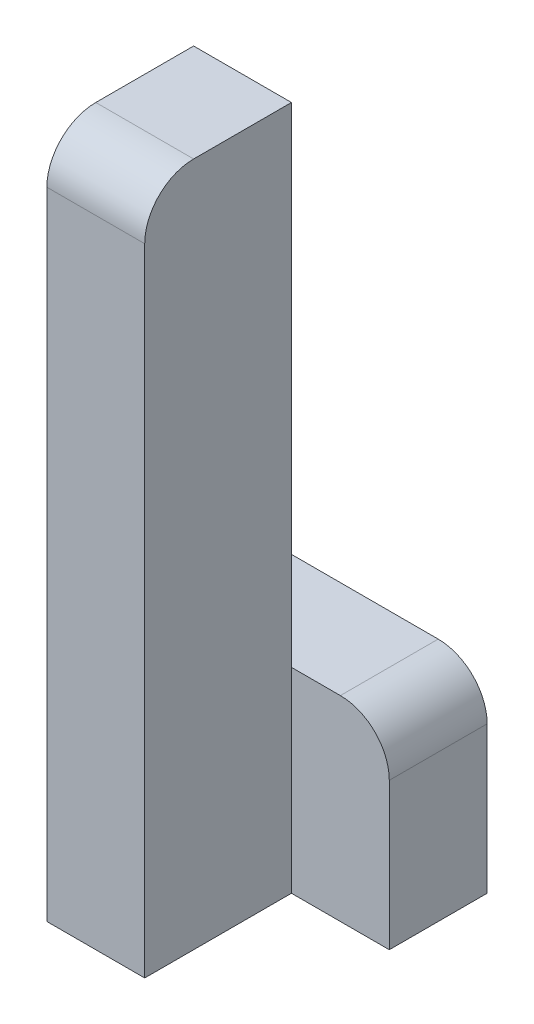
SolidWorks part; units mm, degrees
ref_plane "Front Plane" through (0, 0, 0) normal (0, 0, 1) x (1, 0, 0)
ref_plane "Top Plane" through (0, 0, 0) normal (0, 1, 0) x (1, 0, 0)
ref_plane "Right Plane" through (0, 0, 0) normal (1, 0, 0) x (0, 0, -1)
sketch "Sketch1" plane through (0, 0, 0) normal (0, 0, 1) x (1, 0, 0)
  line L1 (-30, -140) -> (-10, -140)
  line L2 (-10, -140) -> (-10, 0)
  line L3 (-10, 0) -> (-30, 0)
  line L4 (-30, 0) -> (-30, -140)
  dimension "D1" = 20
  dimension "Width" = 140
extrude "Boss-Extrude1" add sketch "Sketch1" along normal blind 30
sketch "Sketch2" plane through (0, 0, 0) normal (0, 0, 1) x (1, 0, 0)
  line L1 (-30, -140) -> (10, -140)
  line L2 (10, -140) -> (10, -100)
  line L3 (10, -100) -> (-30, -100)
  line L4 (-30, -100) -> (-30, -140)
  dimension "D1" = 40
  dimension "Width" = 40
extrude "Boss-Extrude2" add sketch "Sketch2" against normal blind 20
fillet "Fillet1" radius 10 2 edges at (10, -100, -10) (-20, 0, 30)
